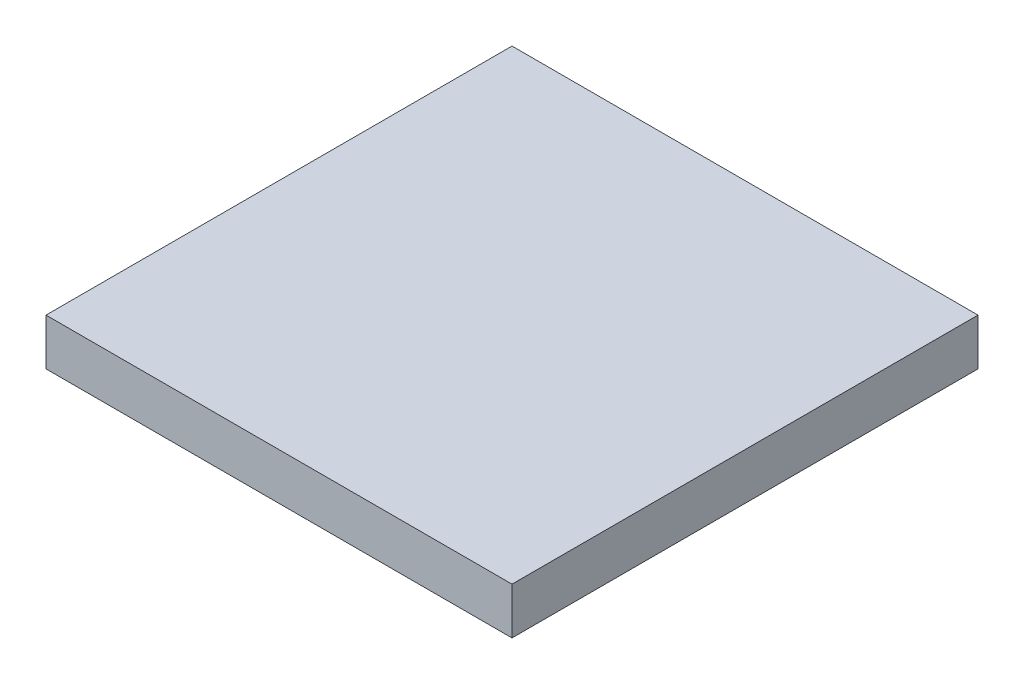
SolidWorks part; units mm, degrees
ref_plane "Front Plane" through (0, 0, 0) normal (0, 0, 1) x (1, 0, 0)
ref_plane "Top Plane" through (0, 0, 0) normal (0, 1, 0) x (1, 0, 0)
ref_plane "Right Plane" through (0, 0, 0) normal (1, 0, 0) x (0, 0, -1)
sketch "Sketch1" plane through (0, 0, 0) normal (0, 1, 0) x (1, 0, 0)
  line L0 (0, 0) -> (18.6879, 0) construction
  line L1 (0, 0) -> (0, -14.4281) construction
  line L3 (-2.5, 2.5) -> (2.5, 2.5)
  line L4 (-2.5, 2.5) -> (-2.5, -2.5)
  line L5 (-2.5, -2.5) -> (2.5, -2.5)
  line L6 (2.5, 2.5) -> (2.5, -2.5)
  dimension "D1" = 5
  dimension "D2" = 5
extrude "Boss-Extrude1" add sketch "Sketch1" along normal blind 0.5
